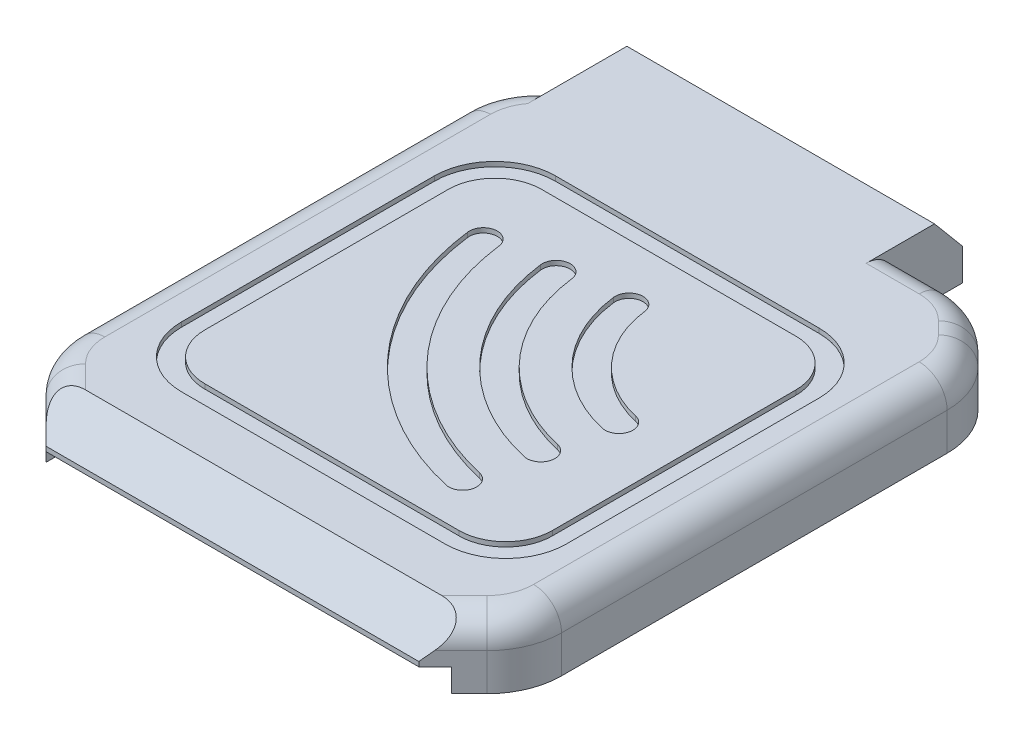
SolidWorks part; units mm, degrees
ref_plane "Front Plane" through (0, 0, 0) normal (0, 0, 1) x (1, 0, 0)
ref_plane "Top Plane" through (0, 0, 0) normal (0, 1, 0) x (1, 0, 0)
ref_plane "Right Plane" through (0, 0, 0) normal (1, 0, 0) x (0, 0, -1)
sketch "Sketch1" plane through (0, 0, 0) normal (0, 1, 0) x (1, 0, 0)
  line L0 (-26, 24) -> (-20, 30)
  line L1 (-20, 30) -> (20, 30)
  line L2 (20, 30) -> (26, 24)
  line L3 (26, 24) -> (26, -24)
  line L4 (26, -24) -> (20, -30)
  line L5 (20, -30) -> (-20, -30)
  line L6 (-20, -30) -> (-26, -24)
  line L7 (-26, -24) -> (-26, 24)
  dimension "D1" = 52
  dimension "D2" = 48
  dimension "D3" = 26
  dimension "D4" = 24
  dimension "D5" = 6
  dimension "D6" = 6
  dimension "D7" = 6
  dimension "D8" = 6
extrude "Boss-Extrude1" add sketch "Sketch1" along normal blind 7
sketch "Sketch2" plane through (0, 0, 0) normal (0, -1, 0) x (1, 0, 0)
  line L0 (26, 24) -> (26, -24) construction
  line L1 (23.5, -19.5) -> (-20, -19.5)
  line L2 (23.5, -19.5) -> (23.5, 22)
  line L3 (23.5, 22) -> (-20, 22)
  line L4 (-20, -19.5) -> (-20, 22)
  line L5 (-26, -24) -> (-26, 24) construction
  line L6 (20, -30) -> (-20, -30) construction
  line L7 (-20, 30) -> (20, 30) construction
  dimension "D1" = 2.5
  dimension "D2" = 6
  dimension "D3" = 10.5
  dimension "D4" = 8
extrude "Cut-Extrude1" cut sketch "Sketch2" against normal offset from surface (6.25 mm away) 0.75 up to face at (0, 7, 0)
sketch "Sketch3" plane through (0, 6.25, 0) normal (0, -1, 0) x (1, 0, 0)
  line L0 (-20, 16) -> (-14, 22)
  line L1 (-20, -19.5) -> (-20, 22) construction
  line L2 (-20, 22) -> (23.5, 22) construction
  line L3 (-14, 22) -> (-20, 22)
  line L4 (-20, 22) -> (-20, 16)
  line L5 (-20, -13.5) -> (-14, -19.5)
  line L6 (-20, -19.5) -> (23.5, -19.5) construction
  line L7 (-14, -19.5) -> (-20, -19.5)
  line L8 (-20, -19.5) -> (-20, -13.5)
  line L9 (17.5, -19.5) -> (23.5, -19.5)
  line L10 (23.5, 22) -> (23.5, -19.5) construction
  line L11 (23.5, -19.5) -> (23.5, 22) construction
  line L12 (23.5, -19.5) -> (23.5, -13.5)
  line L13 (23.5, -13.5) -> (17.5, -19.5)
  line L14 (17.5, 22) -> (23.5, 16)
  line L15 (23.5, 22) -> (-20, 22) construction
  line L16 (23.5, 16) -> (23.5, 22)
  line L17 (23.5, 22) -> (17.5, 22)
  dimension "D1" = 6
  dimension "D2" = 6
  dimension "D3" = 6
  dimension "D4" = 6
extrude "Boss-Extrude2" add sketch "Sketch3" along normal blind 3
sketch "Sketch4" plane through (0, 0, 0) normal (0, -1, 0) x (1, 0, 0)
  line L0 (23.5, 22) -> (-20, 22) construction
  line L1 (-21.5, 38.3269) -> (21.75, 38.3269)
  line L2 (-21.5, 38.3269) -> (-21.5, 22)
  line L3 (-21.5, 22) -> (21.75, 22)
  line L4 (21.75, 38.3269) -> (21.75, 22)
  line L5 (-26, -24) -> (-26, 24) construction
  line L6 (26, 24) -> (26, -24) construction
  dimension "D1" = 4.5
  dimension "D2" = 4.25
extrude "Cut-Extrude2" cut sketch "Sketch4" against normal blind 2.5
sketch "Sketch5" plane through (0, 0, 0) normal (0, -1, 0) x (1, 0, 0)
  line L1 (26, 24) -> (26, -24) construction
  line L3 (-20, 30) -> (20, 30) construction
  line L4 (-26, -24) -> (-26, 24) construction
  line L5 (20, -30) -> (-20, -30) construction
  circle A0 centre (-17, 25.75) radius 1.25
  circle A1 centre (17, 25.75) radius 1.25
  circle A2 centre (17, -25.75) radius 1.25
  dimension "D1" = 4.25
  dimension "D3" = 2.5
  dimension "D2" = 9
  dimension "D4" = 9
  dimension "D6" = 4.25
extrude "Cut-Extrude3" cut sketch "Sketch5" against normal offset from surface (6.5 mm away) 0.5 up to face at (0, 7, 0)
sketch "Sketch6" plane through (0, 6.25, 0) normal (0, -1, 0) x (1, 0, 0)
  line L0 (-20, 22) -> (21.75, 22) construction
  line L1 (-20, 22) -> (23.5, 22)
  line L2 (-20, 22) -> (-20, -19.5)
  line L3 (-20, -19.5) -> (23.5, -19.5)
  line L4 (23.5, 22) -> (23.5, -19.5)
  line L5 (8.5, -4.5) -> (15.5, -4.5)
  line L6 (8.5, -4.5) -> (8.5, -11.5)
  line L7 (8.5, -11.5) -> (15.5, -11.5)
  line L8 (15.5, -4.5) -> (15.5, -11.5)
  line L9 (-20, 22) -> (-20, -19.5) construction
  dimension "D1" = 7
  dimension "D3" = 8
  dimension "D4" = 8
extrude "Boss-Extrude3" add sketch "Sketch6" along normal blind 0.75
sketch "Sketch7" plane through (0, 7, 0) normal (0, 1, 0) x (1, 0, 0)
  line L0 (13.506, 3.3894) -> (-134.27, -644.9749) construction
  line L1 (-6.9433, 9.3186) -> (58.2844, 17.513) construction
  line L3 (15.5, -1013.8483) -> (15.5, 48986.1517) construction
  line L4 (-18.2855, 16.4554) -> (19, 16.4554)
  line L5 (-18.2855, 16.4554) -> (-18.2855, -19.6743)
  line L6 (-7.5977, -8.7765) -> (697.0667, 629.2875) construction
  line L7 (-18.2855, -19.6743) -> (19, -19.6743)
  line L8 (19, 16.4554) -> (19, -19.6743)
  line L9 (21, -21.6743) -> (-20.2855, -21.6743)
  line L10 (21, -21.6743) -> (21, 18.4554)
  line L11 (21, 18.4554) -> (-20.2855, 18.4554)
  line L12 (-20.2855, -21.6743) -> (-20.2855, 18.4554)
  line L14 (26, -24) -> (26, 24) construction
  line L15 (-26, 24) -> (-26, -24) construction
  arc A0 (12.5, -1.0243) -> (2.1053, 10.4554) centre (15.5, 12.1381) cw construction
  arc A1 (0.617, 10.2684) -> (12.1667, -2.4868) centre (15.5, 12.1381) ccw
  arc A2 (3.5936, 10.6424) -> (12.8333, 0.4382) centre (15.5, 12.1381) ccw
  arc A3 (3.5936, 10.6424) -> (0.617, 10.2684) centre (2.1053, 10.4554) ccw
  arc A4 (12.1667, -2.4868) -> (12.8333, 0.4382) centre (12.5, -1.0243) ccw
  arc A5 (-4.8401, 9.5829) -> (10.9444, -7.8493) centre (15.5, 12.1381) ccw construction
  arc A6 (-6.3284, 9.3959) -> (10.6111, -9.3118) centre (15.5, 12.1381) ccw
  arc A7 (-3.3518, 9.7698) -> (11.2778, -6.3868) centre (15.5, 12.1381) ccw
  arc A8 (-3.3518, 9.7698) -> (-6.3284, 9.3959) centre (-4.8401, 9.5829) ccw
  arc A9 (10.6111, -9.3118) -> (11.2778, -6.3868) centre (10.9444, -7.8493) ccw
  arc A10 (9.3889, -14.6743) -> (-11.7855, 8.7103) centre (15.5, 12.1381) cw construction
  arc A11 (-13.2738, 8.5234) -> (9.0556, -16.1367) centre (15.5, 12.1381) ccw
  arc A12 (-10.2972, 8.8973) -> (9.7222, -13.2118) centre (15.5, 12.1381) ccw
  arc A13 (-10.2972, 8.8973) -> (-13.2738, 8.5234) centre (-11.7855, 8.7103) ccw
  arc A14 (9.0556, -16.1367) -> (9.7222, -13.2118) centre (9.3889, -14.6743) ccw
  point P0 (15.5, 12.1381)
  point P4 (5.4929, 3.0768)
  point P9 (0.304, -1.6216)
  point P17 (-4.8849, -6.3201)
  dimension "D1" = 1.5
  dimension "D2" = 1.5
  dimension "D3" = 1.5
  dimension "D4" = 12
  dimension "D5" = 4
  dimension "D6" = 4
  dimension "D13" = 6.5
  dimension "D15" = 6
  dimension "D12" = 6.5
  dimension "D7" = 35
  dimension "D8" = 2
  dimension "D9" = 2
  dimension "D10" = 2
  dimension "D11" = 2
  dimension "D14" = 5
  dimension "D16" = 3.5
  dimension "D17" = 5
  dimension "D18" = 5.7145
extrude "Cut-Extrude4" cut sketch "Sketch7" against normal blind 0.5 contours A1 A4 A2 A3 | A6 A9 A7 A8 | A11 A14 A12 A13 | L12 L9 L10 L11 L4 L8 L7 L5
chamfer "Chamfer1" distance 4 angle 40 1 edges at (0, 7, 30)
fillet "Fillet1" radius 8 6 edges at (20, 3.5, -30) (26, 3.5, -24) (26, 3.5, 24) (-20, 3.5, -30) (-26, 3.5, -24) (-26, 3.5, 24)
fillet "Fillet2" radius 3 13 edges at (23.5066, 7, 26.4934) (25.391, 7, 23.7478) (26, 7, 0) (25.391, 7, -23.7478) (23, 7, -27) (19.7478, 7, -29.391) (0, 7, -30) (-19.7478, 7, -29.391) (-23, 7, -27) (-25.391, 7, -23.7478) (-23.5066, 7, 26.4934) (-25.391, 7, 23.7478) (-26, 7, 0)
fillet "Fillet3" radius 5 4 edges at (-18.2855, 6.75, 19.6743) (19, 6.75, 19.6743) (19, 6.75, -16.4554) (-18.2855, 6.75, -16.4554)
fillet "Fillet4" radius 6.5 4 edges at (-20.2855, 6.75, -18.4554) (21, 6.75, -18.4554) (21, 6.75, 21.6743) (-20.2855, 6.75, 21.6743)
sketch "Sketch11" plane through (0, 7, 0) normal (0, 1, 0) x (1, 0, 0)
  line L0 (-22, 23.7574) -> (-22, 37.35)
  line L1 (-22, 37.35) -> (11, 37.35)
  line L2 (11, 37.35) -> (11, 23.7574)
  line L3 (11, 23.7574) -> (-22, 23.7574)
  line L4 (-26, -20.6863) -> (-26, 20.6863) construction
  line L5 (-20.2218, 25.5355) -> (-21.5355, 24.2218) construction
  line L6 (-16.6863, 30) -> (16.6863, 30) construction
  dimension "D1" = 4
  dimension "D2" = 33
  dimension "D3" = 7.35
extrude "Boss-Extrude4" add sketch "Sketch11" against normal up to surface (7 mm away) up to face at (17, 0, -27)
chamfer "Chamfer2" distance 3.6 angle 40 1 edges at (-5.5, 7, -37.35)
sketch "Sketch12" plane through (0, 0, 0) normal (0, -1, 0) x (1, 0, 0)
  line L0 (-20, -19.5) -> (23.5, -19.5) construction
  line L1 (9, -19.5) -> (-20, -19.5)
  line L2 (9, -19.5) -> (9, -37.35)
  line L3 (9, -37.35) -> (-20, -37.35)
  line L4 (-20, -19.5) -> (-20, -37.35)
  line L5 (11, -30) -> (11, -37.35) construction
  line L8 (-20, 22) -> (-20, -19.5) construction
  line L9 (11, -37.35) -> (-22, -37.35) construction
  dimension "D1" = 2
extrude "Cut-Extrude7" cut sketch "Sketch12" against normal up to surface (5.5 mm away)
